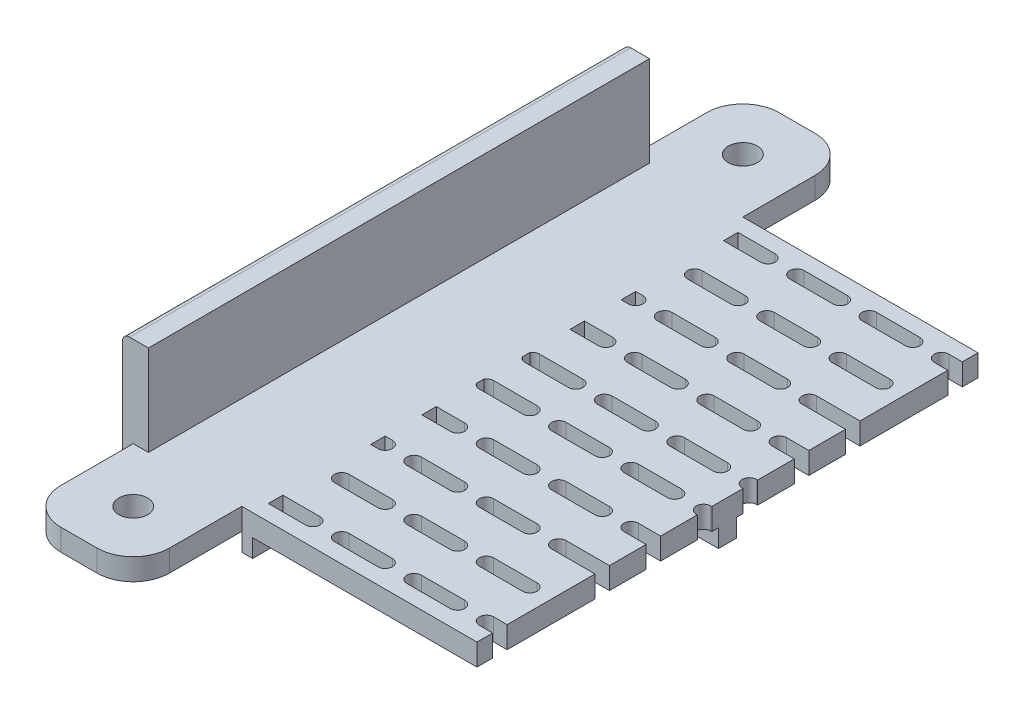
SolidWorks part; units mm, degrees
ref_plane "前视基准面" through (0, 0, 0) normal (0, 0, 1) x (1, 0, 0)
ref_plane "上视基准面" through (0, 0, 0) normal (0, 1, 0) x (1, 0, 0)
ref_plane "右视基准面" through (0, 0, 0) normal (1, 0, 0) x (0, 0, -1)
sketch "草图1" plane through (0, 0, 0) normal (0, 1, 0) x (1, 0, 0)
  line L0 (95.5, 69.25) -> (95.5, -69.25)
  line L1 (90.5, 64.25) -> (-90.5, 64.25)
  line L2 (90.5, 64.25) -> (90.5, -64.25)
  line L3 (90.5, -64.25) -> (-90.5, -64.25)
  line L4 (-90.5, 64.25) -> (-90.5, -64.25)
  line L5 (90.5, 64.25) -> (-90.5, -64.25) construction
  line L6 (90.5, -64.25) -> (-90.5, 64.25) construction
  line L7 (95.5, -69.25) -> (-95.5, -69.25)
  line L8 (-95.5, 69.25) -> (-95.5, -69.25)
  line L9 (95.5, 69.25) -> (-95.5, 69.25)
  point P0 (0, 0)
  dimension "D1" = 5
extrude "凸台-拉伸1" add sketch "草图1" along normal blind 20
sketch "草图2" plane through (0, 0, 0) normal (0, -1, 0) x (1, 0, 0)
  line L4 (-95.5, -69.25) -> (95.5, -69.25)
  line L5 (95.5, -69.25) -> (95.5, 69.25)
  line L6 (95.5, 69.25) -> (-95.5, 69.25)
  line L7 (-95.5, 69.25) -> (-95.5, -69.25)
  line L8 (-95.5, -69.25) -> (95.5, -69.25)
  line L9 (95.5, -69.25) -> (95.5, 69.25)
  line L10 (95.5, 69.25) -> (-95.5, 69.25)
  line L11 (-95.5, 69.25) -> (-95.5, -69.25)
  dimension "D1" = 0
extrude "凸台-拉伸2" add sketch "草图2" along normal blind 5
sketch "草图3" plane through (0, 0, -64.25) normal (0, 0, 1) x (1, 0, 0)
  line L4 (-90.5, 0) -> (90.5, 0)
  line L5 (90.5, 0) -> (90.5, 20)
  line L6 (90.5, 20) -> (-90.5, 20)
  line L7 (-90.5, 20) -> (-90.5, 0)
  line L8 (-90.5, 0) -> (90.5, 0)
  line L9 (90.5, 0) -> (90.5, 20)
  line L10 (90.5, 20) -> (-90.5, 20)
  line L11 (-90.5, 20) -> (-90.5, 0)
  dimension "D1" = 0
extrude "切除-拉伸1" cut sketch "草图3" against normal blind 49 and the other way blind 153
sketch "草图4" plane through (0, -5, 0) normal (0, -1, 0) x (1, 0, 0)
  line L0 (-95.5, 0) -> (-47.5, 0) construction
  line L1 (-47.5, 103) -> (47.5, 103) construction
  line L2 (-47.5, 103) -> (-47.5, -103) construction
  line L3 (-47.5, -103) -> (47.5, -103) construction
  line L4 (47.5, 103) -> (47.5, -103) construction
  line L5 (-47.5, 103) -> (47.5, -103) construction
  line L6 (-47.5, -103) -> (47.5, 103) construction
  line L7 (-95.5, 69.25) -> (-95.5, -69.25) construction
  line L8 (-95.5, 0) -> (-95.5, -35)
  line L9 (-95.5, -35) -> (-90.5, -35)
  line L10 (-90.5, -35) -> (-90.5, 35)
  line L11 (-90.5, 35) -> (-95.5, 35)
  line L12 (-95.5, 35) -> (-95.5, 0)
  line L13 (0, 0) -> (0, 35) construction
  line L14 (95.5, 35) -> (95.5, 0)
  line L15 (90.5, 35) -> (95.5, 35)
  line L16 (90.5, -35) -> (90.5, 35)
  line L17 (95.5, -35) -> (90.5, -35)
  line L18 (95.5, 0) -> (95.5, -35)
  point P0 (0, 0)
extrude "凸台-拉伸3" add sketch "草图4" along normal blind 49
sketch "草图5" plane through (0, -54, 0) normal (0, -1, 0) x (1, 0, 0)
  line L4 (-95.5, 35) -> (-95.5, -35)
  line L5 (-95.5, -35) -> (-90.5, -35)
  line L6 (-90.5, -35) -> (-90.5, 35)
  line L7 (-90.5, 35) -> (-95.5, 35)
  line L8 (-95.5, 35) -> (-95.5, -35)
  line L9 (-95.5, -35) -> (-90.5, -35)
  line L10 (-90.5, -35) -> (-90.5, 35)
  line L11 (-90.5, 35) -> (-95.5, 35)
  line L12 (95.5, 35) -> (90.5, 35)
  line L13 (90.5, 35) -> (90.5, -35)
  line L14 (90.5, -35) -> (95.5, -35)
  line L15 (95.5, -35) -> (95.5, 35)
  line L16 (95.5, 35) -> (90.5, 35)
  line L17 (90.5, 35) -> (90.5, -35)
  line L18 (90.5, -35) -> (95.5, -35)
  line L19 (95.5, -35) -> (95.5, 35)
  dimension "D1" = 0
  dimension "D2" = 0
extrude "凸台-拉伸4" add sketch "草图5" along normal blind 34
sketch "草图7" plane through (-95.5, 0, 0) normal (-1, 0, 0) x (0, 0, 1)
  line L0 (35, -88) -> (-35, -88)
  line L1 (-35, -88) -> (-35, -83)
  line L2 (-35, -88) -> (-35, -5) construction
  line L3 (-35, -83) -> (35, -83)
  line L4 (35, -88) -> (35, -5) construction
  line L5 (35, -83) -> (35, -88)
extrude "凸台-拉伸5" add sketch "草图7" along normal blind 37
sketch "草图8" plane through (95.5, 0, 0) normal (1, 0, 0) x (0, 0, -1)
  line L4 (-35, -83) -> (-35, -88)
  line L5 (35, -83) -> (-35, -83)
  line L6 (35, -88) -> (35, -83)
  line L7 (-35, -88) -> (35, -88)
  line L8 (-35, -83) -> (-35, -88)
  line L9 (35, -83) -> (-35, -83)
  line L10 (35, -88) -> (35, -83)
  line L11 (-35, -88) -> (35, -88)
  dimension "D1" = 0
extrude "凸台-拉伸6" add sketch "草图8" along normal blind 37
sketch "草图12" plane through (0, -5, 0) normal (0, -1, 0) x (1, 0, 0)
  line L0 (0, 0) -> (0, -50.9491) construction
  line L1 (0, 0) -> (21.7152, 0) construction
  line L6 (90.5, 35) -> (95.5, 35)
  line L7 (90.5, 35) -> (95.5, 35)
  line L8 (95.5, -69.25) -> (95.5, -35)
  line L9 (95.5, -35) -> (90.5, -35)
  line L10 (90.5, -35) -> (90.5, 35)
  line L11 (95.5, 35) -> (95.5, 69.25)
  line L15 (95.5, -35) -> (90.5, -35) construction
  line L16 (90.5, -35) -> (90.5, 35) construction
  line L20 (95.5, -69.25) -> (95.5, -35)
  line L27 (95.5, 35) -> (95.5, 69.25)
  line L28 (95.5, 69.25) -> (-95.5, 69.25)
  line L29 (95.5, 69.25) -> (-95.5, 69.25)
  line L30 (-95.5, 69.25) -> (-95.5, 35)
  line L31 (-95.5, 69.25) -> (-95.5, 35)
  line L32 (-95.5, 35) -> (-90.5, 35)
  line L33 (-95.5, 35) -> (-90.5, 35)
  line L34 (-90.5, 35) -> (-90.5, -35)
  line L35 (-90.5, 35) -> (-90.5, -35)
  line L36 (-90.5, -35) -> (-95.5, -35)
  line L37 (-90.5, -35) -> (-95.5, -35)
  line L38 (-95.5, -35) -> (-95.5, -69.25)
  line L39 (-95.5, -35) -> (-95.5, -69.25)
  line L40 (-95.5, -69.25) -> (95.5, -69.25)
  line L41 (-95.5, -69.25) -> (95.5, -69.25)
  circle A0 centre (48, -35) radius 12.5
  circle A1 centre (-48, -35) radius 12.5
  circle A2 centre (48, 35) radius 12.5
  circle A3 centre (-48, 35) radius 12.5
  dimension "D1" = 0
sketch "草图16" plane through (0, -88, 0) normal (0, -1, 0) x (1, 0, 0)
  line L0 (132.5, 35) -> (117.5, 35)
  line L1 (132.5, 35) -> (90.5, 35) construction
  line L2 (117.5, 35) -> (117.5, -35)
  line L3 (90.5, -35) -> (132.5, -35) construction
  line L4 (117.5, -35) -> (132.5, -35)
  line L5 (132.5, -35) -> (132.5, 35)
  line L6 (-132.5, -35) -> (-117.5, -35)
  line L7 (-132.5, -35) -> (-90.5, -35) construction
  line L8 (-117.5, -35) -> (-117.5, 35)
  line L9 (-90.5, 35) -> (-132.5, 35) construction
  line L10 (-117.5, 35) -> (-132.5, 35)
  line L11 (-132.5, 35) -> (-132.5, -35)
extrude "切除-拉伸7" cut sketch "草图16" against normal blind 62
extrude "切除-拉伸9" cut sketch "草图12" against normal blind 20 contours A0 | A1 | A3 | A2
sketch "草图19" plane through (117.5, 0, 0) normal (1, 0, 0) x (0, 0, -1)
  line L4 (-35, -83) -> (-35, -88)
  line L5 (-35, -88) -> (35, -88)
  line L6 (35, -88) -> (35, -83)
  line L7 (35, -83) -> (-35, -83)
  line L8 (-35, -83) -> (-35, -88)
  line L9 (-35, -88) -> (35, -88)
  line L10 (35, -88) -> (35, -83)
  line L11 (35, -83) -> (-35, -83)
  dimension "D1" = 0
extrude "切除-拉伸10" cut sketch "草图19" against normal blind 3.5
sketch "草图20" plane through (-117.5, 0, 0) normal (-1, 0, 0) x (0, 0, 1)
  line L4 (-35, -83) -> (-35, -88)
  line L5 (-35, -88) -> (35, -88)
  line L6 (35, -88) -> (35, -83)
  line L7 (35, -83) -> (-35, -83)
  line L8 (-35, -83) -> (-35, -88)
  line L9 (-35, -88) -> (35, -88)
  line L10 (35, -88) -> (35, -83)
  line L11 (35, -83) -> (-35, -83)
  dimension "D1" = 0
extrude "切除-拉伸11" cut sketch "草图20" against normal blind 3.5
sketch "草图21" plane through (0, -83, 0) normal (0, 1, 0) x (1, 0, 0)
  line L0 (-114, 0) -> (-95.5, 0) construction
  line L1 (-114, -35) -> (-114, 35) construction
  line L2 (-95.5, -35) -> (-95.5, 35) construction
  line L3 (-104.75, 0) -> (-104.75, -35) construction
  line L4 (-114, -35) -> (-95.5, -35) construction
  line L5 (0, 0) -> (0, 27.7926) construction
  circle A0 centre (-104.75, -17.5) radius 4
  circle A1 centre (-104.75, 17.5) radius 4
  circle A2 centre (104.75, -17.5) radius 4
  circle A3 centre (104.75, 17.5) radius 4
extrude "切除-拉伸12" cut sketch "草图21" against normal through all
fillet "圆角5" radius 10 4 edges at (114, -85.5, -35) (114, -85.5, 35) (-114, -85.5, 35) (-114, -85.5, -35)
sketch "草图22" plane through (90.5, 0, 0) normal (-1, 0, 0) x (0, 0, 1)
  line L6 (35, -88) -> (35, -5)
  line L7 (35, -5) -> (-35, -5)
  line L10 (-35, -5) -> (-35, -88)
  line L11 (-35, -88) -> (35, -88)
  line L12 (35, -88) -> (35, -5)
  line L13 (35, -5) -> (-35, -5)
  line L16 (-35, -5) -> (-35, -88)
  line L17 (-35, -88) -> (35, -88)
  dimension "D1" = 0
extrude "切除-拉伸13" cut sketch "草图22" against normal blind 54
sketch "草图23" plane through (-90.5, 0, 0) normal (1, 0, 0) x (0, 0, -1)
  line L6 (35, -5) -> (-35, -5)
  line L7 (-35, -5) -> (-35, -88)
  line L8 (-35, -88) -> (35, -88)
  line L9 (35, -88) -> (35, -5)
  line L12 (35, -5) -> (-35, -5)
  line L13 (-35, -5) -> (-35, -88)
  line L14 (-35, -88) -> (35, -88)
  line L15 (35, -88) -> (35, -5)
  dimension "D1" = 0
extrude "切除-拉伸14" cut sketch "草图23" against normal blind 54
sketch "草图24" plane through (0, -5, 0) normal (0, -1, 0) x (1, 0, 0)
  circle A1 centre (80.5, 18.25) radius 2
  circle A3 centre (80.5, -19.75) radius 2
extrude "切除-拉伸15" cut sketch "草图24" against normal blind 10
sketch "草图25" plane through (0, 0, 0) normal (0, 1, 0) x (1, 0, 0)
  circle A0 centre (80.5, -18.25) radius 4
  circle A1 centre (80.5, 19.75) radius 4
sketch "草图26" plane through (0, 0, 0) normal (0, 1, 0) x (1, 0, 0)
  line L4 (90.5, -69.25) -> (90.5, 69.25)
  line L5 (90.5, 69.25) -> (-90.5, 69.25)
  line L6 (-90.5, 69.25) -> (-90.5, -69.25)
  line L7 (-90.5, -69.25) -> (90.5, -69.25)
  line L8 (90.5, -69.25) -> (90.5, 69.25)
  line L9 (90.5, 69.25) -> (-90.5, 69.25)
  line L10 (-90.5, 69.25) -> (-90.5, -69.25)
  line L11 (-90.5, -69.25) -> (90.5, -69.25)
  circle A0 centre (48, -35) radius 12.5 construction
  circle A1 centre (48, -35) radius 12.5
  circle A2 centre (48, 35) radius 12.5 construction
  circle A3 centre (48, 35) radius 12.5
  circle A4 centre (-48, -35) radius 12.5 construction
  circle A5 centre (-48, -35) radius 12.5
  circle A6 centre (-48, 35) radius 12.5 construction
  circle A7 centre (-48, 35) radius 12.5
  dimension "D1" = 0
extrude "凸台-拉伸8" add sketch "草图26" along normal blind 1
extrude "切除-拉伸16" cut sketch "草图25" along normal blind 1 and the other way blind 4
mirror "镜向1" about plane through (0, 0, 0) normal (1, 0, 0) of "切除-拉伸15", "切除-拉伸16"
sketch "草图28" plane through (0, 1, 0) normal (0, 1, 0) x (1, 0, 0)
  circle A0 centre (-80.5, -18.25) radius 4 construction
  circle A1 centre (-80.5, -18.25) radius 4
  circle A2 centre (-80.5, 19.75) radius 4 construction
  circle A3 centre (-80.5, 19.75) radius 4
  circle A4 centre (80.5, -18.25) radius 4 construction
  circle A5 centre (80.5, -18.25) radius 4
  circle A6 centre (80.5, 19.75) radius 4 construction
  circle A7 centre (80.5, 19.75) radius 4
extrude "凸台-拉伸9" add sketch "草图28" against normal up to surface (6 mm away) up to face at (-80.5, -5, 16.25)
sketch "草图29" plane through (0, -5, 0) normal (0, -1, 0) x (1, 0, 0)
  line L0 (95.5, 69.25) -> (95, 69.25)
  line L1 (-95, 0) -> (-95, 69.25)
  line L2 (95.5, 69.25) -> (-95.5, 69.25) construction
  line L3 (-95, 69.25) -> (-95.5, 69.25)
  line L4 (-95.5, 69.25) -> (-95.5, -69.25)
  line L5 (-95.5, -69.25) -> (-95, -69.25)
  line L6 (-95.5, -69.25) -> (95.5, -69.25) construction
  line L7 (-95, -69.25) -> (-95, 0)
  line L8 (95, 69.25) -> (95, -69.25)
  line L9 (95, -69.25) -> (95.5, -69.25)
  line L10 (95.5, -69.25) -> (95.5, 69.25)
extrude "切除-拉伸18" cut sketch "草图29" against normal blind 50
sketch "草图31" plane through (0, -5, 0) normal (0, -1, 0) x (1, 0, 0)
  line L0 (-95, 69.25) -> (-95, 89.25)
  line L1 (-85, 99.25) -> (-75, 99.25)
  line L2 (-65, 89.25) -> (-65, 69.25)
  line L3 (95, 69.25) -> (-95, 69.25) construction
  line L4 (-65, 69.25) -> (-95, 69.25)
  line L5 (-80, 99.25) -> (-80, 69.25) construction
  line L6 (-80, 84.25) -> (-65, 84.25) construction
  line L7 (0, 0) -> (19.0311, 0) construction
  line L8 (0, 0) -> (0, -16.3488) construction
  line L9 (-65, -89.25) -> (-65, -69.25)
  line L10 (-85, -99.25) -> (-75, -99.25)
  line L11 (-95, -69.25) -> (-95, -89.25)
  line L12 (-65, -69.25) -> (-95, -69.25)
  line L13 (80, 84.25) -> (65, 84.25) construction
  line L14 (80, 99.25) -> (80, 69.25) construction
  line L15 (65, -69.25) -> (95, -69.25)
  line L16 (95, -69.25) -> (95, -89.25)
  line L17 (85, -99.25) -> (75, -99.25)
  line L18 (65, -89.25) -> (65, -69.25)
  line L19 (65, 69.25) -> (95, 69.25)
  line L20 (65, 89.25) -> (65, 69.25)
  line L21 (85, 99.25) -> (75, 99.25)
  line L22 (95, 69.25) -> (95, 89.25)
  arc A0 (-65, 89.25) -> (-75, 99.25) centre (-75, 89.25) ccw
  arc A1 (-95, 89.25) -> (-85, 99.25) centre (-85, 89.25) cw
  circle A2 centre (-80, 84.25) radius 4
  circle A3 centre (-80, -84.25) radius 4
  arc A4 (-65, -89.25) -> (-75, -99.25) centre (-75, -89.25) cw
  arc A5 (-95, -89.25) -> (-85, -99.25) centre (-85, -89.25) ccw
  arc A6 (95, -89.25) -> (85, -99.25) centre (85, -89.25) cw
  arc A7 (65, -89.25) -> (75, -99.25) centre (75, -89.25) ccw
  circle A8 centre (80, -84.25) radius 4
  circle A9 centre (80, 84.25) radius 4
  arc A10 (95, 89.25) -> (85, 99.25) centre (85, 89.25) ccw
  arc A11 (65, 89.25) -> (75, 99.25) centre (75, 89.25) cw
  dimension "D1" = 10
extrude "凸台-拉伸10" add sketch "草图31" against normal up to surface (6 mm away) up to face at (-48, 1, 47.5)
sketch "草图32" plane through (0, 20, 0) normal (0, 1, 0) x (1, 0, 0)
  line L0 (90.5, 69.25) -> (91.3, 69.25)
  line L4 (95, 69.25) -> (90.5, 69.25) construction
  line L5 (90.5, -69.25) -> (90.5, 69.25) construction
  line L6 (90.5, -69.25) -> (90.5, 69.25)
  line L7 (91.3, 69.25) -> (91.3, -69.25)
  line L8 (90.5, -69.25) -> (95, -69.25) construction
  line L9 (91.3, -69.25) -> (90.5, -69.25)
  line L10 (-90.5, -69.25) -> (-91.3, -69.25)
  line L11 (-95, -69.25) -> (-90.5, -69.25) construction
  line L12 (-91.3, -69.25) -> (-91.3, 69.25)
  line L13 (-90.5, 69.25) -> (-95, 69.25) construction
  line L14 (-91.3, 69.25) -> (-90.5, 69.25)
  line L15 (-90.5, 69.25) -> (-90.5, -69.25) construction
  line L16 (-90.5, 69.25) -> (-90.5, -69.25)
extrude "切除-拉伸19" cut sketch "草图32" against normal up to surface (19 mm away) up to face at (-48, 1, 47.5)
sketch "草图33" plane through (0, 20, 0) normal (0, 1, 0) x (1, 0, 0)
  line L4 (91.3, 69.25) -> (91.3, -69.25)
  line L5 (91.3, -69.25) -> (95, -69.25)
  line L6 (95, -69.25) -> (95, 69.25)
  line L7 (95, 69.25) -> (91.3, 69.25)
  line L8 (91.3, 69.25) -> (91.3, -69.25)
  line L9 (91.3, -69.25) -> (95, -69.25)
  line L10 (95, -69.25) -> (95, 69.25)
  line L11 (95, 69.25) -> (91.3, 69.25)
  line L12 (-91.3, -69.25) -> (-91.3, 69.25)
  line L13 (-91.3, 69.25) -> (-95, 69.25)
  line L14 (-95, 69.25) -> (-95, -69.25)
  line L15 (-95, -69.25) -> (-91.3, -69.25)
  line L16 (-91.3, -69.25) -> (-91.3, 69.25)
  line L17 (-91.3, 69.25) -> (-95, 69.25)
  line L18 (-95, 69.25) -> (-95, -69.25)
  line L19 (-95, -69.25) -> (-91.3, -69.25)
  dimension "D1" = 0
  dimension "D2" = 0
extrude "凸台-拉伸11" add sketch "草图33" along normal blind 6
sketch "草图34" plane through (0, -5, 0) normal (0, -1, 0) x (1, 0, 0)
  circle A0 centre (-48, -35) radius 12.5 construction
  circle A1 centre (-48, -35) radius 12.5
  circle A2 centre (-48, 35) radius 12.5 construction
  circle A3 centre (-48, 35) radius 12.5
  circle A4 centre (48, -35) radius 12.5 construction
  circle A5 centre (48, -35) radius 12.5
  circle A6 centre (48, 35) radius 12.5 construction
  circle A7 centre (48, 35) radius 12.5
extrude "凸台-拉伸12" add sketch "草图34" against normal up to surface (6 mm away) up to face at (0, 1, 0)
sketch "草图35" plane through (0, -5, 0) normal (0, -1, 0) x (1, 0, 0)
  line L0 (65, -69.25) -> (62, -69.25)
  line L2 (65, 69.25) -> (65, -69.25)
  line L6 (-65, -69.25) -> (65, -69.25) construction
  line L8 (62, -69.25) -> (62, 69.25)
  line L9 (65, 69.25) -> (-65, 69.25) construction
  line L10 (62, 69.25) -> (65, 69.25)
  line L11 (-65, -69.25) -> (-62, -69.25)
  line L12 (-62, -69.25) -> (-62, 69.25)
  line L13 (-62, 69.25) -> (-65, 69.25)
  line L14 (-65, 69.25) -> (-65, 89.25) construction
  line L15 (-65, 69.25) -> (-65, -69.25)
  point P0 (0, 0)
extrude "凸台-拉伸13" add sketch "草图35" along normal blind 5
sketch "草图36" plane through (-95, 0, 0) normal (-1, 0, 0) x (0, 0, 1)
  line L0 (-69.25, -10) -> (-69.25, -5) construction
  line L1 (-69.25, -10) -> (-69.25, -5)
  line L2 (69.25, -10) -> (69.25, -5) construction
  line L3 (69.25, -10) -> (69.25, -5)
  line L7 (-69.25, 26) -> (69.25, 26) construction
  line L8 (-69.25, 26) -> (69.25, 26)
  line L9 (69.25, 26) -> (69.25, 1) construction
  line L10 (69.25, 26) -> (69.25, 1)
  line L13 (-69.25, -10) -> (69.25, -10)
  line L16 (-69.25, 26) -> (-69.25, 1) construction
  line L17 (-69.25, 26) -> (-69.25, 1)
  line L18 (-69.25, 1) -> (-69.25, -5)
  line L19 (69.25, -5) -> (69.25, 1)
extrude "凸台-拉伸14" add sketch "草图36" along normal blind 3
sketch "草图37" plane through (-95, 0, 0) normal (1, 0, 0) x (0, 0, -1)
  line L4 (69.25, -5) -> (-69.25, -5)
  line L5 (-69.25, -5) -> (-69.25, -10)
  line L6 (-69.25, -10) -> (69.25, -10)
  line L7 (69.25, -10) -> (69.25, -5)
  line L8 (69.25, -5) -> (-69.25, -5)
  line L9 (-69.25, -5) -> (-69.25, -10)
  line L10 (-69.25, -10) -> (69.25, -10)
  line L11 (69.25, -10) -> (69.25, -5)
  dimension "D1" = 0
extrude "切除-拉伸20" cut sketch "草图37" against normal blind 0.5
mirror "镜向2" about plane through (0, 0, 0) normal (1, 0, 0) of "切除-拉伸20", "凸台-拉伸14"
sketch "草图38" plane through (0, -5, 0) normal (0, -1, 0) x (1, 0, 0)
  line L2 (0, 0) -> (62, 0)
  line L3 (62, 69.25) -> (62, -69.25) construction
  line L4 (0, -2.5) -> (-62, -2.5)
  line L5 (0, -2.5) -> (62, -2.5)
  line L6 (0, 2.5) -> (-62, 2.5)
  line L7 (0, 2.5) -> (62, 2.5)
  line L8 (-62, -69.25) -> (-62, 69.25) construction
  line L9 (-62, -2.5) -> (-62, 2.5)
  line L10 (62, 69.25) -> (62, -69.25) construction
  line L11 (62, 2.5) -> (62, -2.5)
  line L12 (0, 0) -> (-62, 0) construction
  dimension "D1" = 2.5
  dimension "D2" = 2.5
extrude "凸台-拉伸15" add sketch "草图38" along normal up to surface (5 mm away) contours L6 L9 L4 L5 L11 L7 up to face at (-63.5, -10, 0)
sketch "草图40" plane through (0, -5, 0) normal (0, -1, 0) x (1, 0, 0)
  line L0 (0, 0) -> (0, 69.25) construction
  line L1 (62, 69.25) -> (-62, 69.25) construction
  line L2 (0, 34.625) -> (-12, 34.625) construction
  line L3 (0, 34.625) -> (-32.125, 2.5) construction
  line L4 (0, 32.625) -> (-12, 32.625)
  line L5 (0, 36.625) -> (-12, 36.625)
  line L6 (62, 2.5) -> (-62, 2.5) construction
  line L7 (25, 34.625) -> (13, 34.625) construction
  line L8 (25, 32.625) -> (13, 32.625)
  line L9 (25, 36.625) -> (13, 36.625)
  line L10 (50, 34.625) -> (38, 34.625) construction
  line L11 (50, 32.625) -> (38, 32.625)
  line L12 (50, 36.625) -> (38, 36.625)
  line L13 (-25, 34.625) -> (-37, 34.625) construction
  line L14 (-25, 32.625) -> (-37, 32.625)
  line L15 (-25, 36.625) -> (-37, 36.625)
  arc A0 (0, 32.625) -> (0, 36.625) centre (0, 34.625) ccw
  arc A1 (-12, 36.625) -> (-12, 32.625) centre (-12, 34.625) ccw
  arc A2 (25, 32.625) -> (25, 36.625) centre (25, 34.625) ccw
  arc A3 (13, 36.625) -> (13, 32.625) centre (13, 34.625) ccw
  arc A4 (50, 32.625) -> (50, 36.625) centre (50, 34.625) ccw
  arc A5 (38, 36.625) -> (38, 32.625) centre (38, 34.625) ccw
  arc A6 (-25, 32.625) -> (-25, 36.625) centre (-25, 34.625) ccw
  arc A7 (-37, 36.625) -> (-37, 32.625) centre (-37, 34.625) ccw
  point P9 (-6, 34.625)
  point P20 (19, 34.625)
  point P27 (44, 34.625)
  point P34 (-31, 34.625)
  dimension "D1" = 45
  dimension "D2" = 3
  dimension "D3" = 2
extrude "切除-拉伸22" cut sketch "草图40" against normal through all contours L5 A1 L4 A0
sketch "草图41" plane through (0, -5, 0) normal (0, -1, 0) x (1, 0, 0)
  line L0 (0, 0) -> (0, 69.25)
  line L1 (62, 69.25) -> (-62, 69.25) construction
  line L2 (0, 34.625) -> (-32.125, 2.5)
  line L3 (62, 2.5) -> (-62, 2.5) construction
  dimension "D1" = 45
pattern_linear "阵列(线性)1" count 3 spacing 20 along (-0.7071, 0, -0.7071) of "切除-拉伸22"
pattern_linear "阵列(线性)2" count 3 spacing 20 along (0.7071, 0, 0.7071) of "切除-拉伸22"
pattern_linear "阵列(线性)3" count 5 spacing 20 along (1, 0, 0) of "阵列(线性)2", "阵列(线性)1", "切除-拉伸22"
sketch "草图42" plane through (0, 1, 0) normal (0, 1, 0) x (1, 0, 0)
  line L0 (82.1421, -50.7671) -> (91.3, -50.7671) construction
  line L1 (82.1421, -50.7671) -> (91.3, -50.7671)
  line L2 (82.1421, -46.7671) -> (91.3, -46.7671) construction
  line L3 (82.1421, -46.7671) -> (91.3, -46.7671)
  line L4 (94.1421, -46.7671) -> (91.3, -46.7671) construction
  line L5 (94.1421, -46.7671) -> (91.3, -46.7671)
  line L6 (94.1421, -50.7671) -> (91.3, -50.7671) construction
  line L7 (94.1421, -50.7671) -> (91.3, -50.7671)
  line L8 (98, -64.9093) -> (96.2843, -64.9093) construction
  line L9 (98, -64.9093) -> (96.2843, -64.9093)
  line L10 (98, -60.9093) -> (96.2843, -60.9093) construction
  line L11 (98, -60.9093) -> (96.2843, -60.9093)
  line L12 (98, -64.9093) -> (98, -60.9093) construction
  line L13 (98, -64.9093) -> (98, -60.9093)
  line L14 (76.2843, -60.9093) -> (88.2843, -60.9093) construction
  line L15 (76.2843, -60.9093) -> (88.2843, -60.9093)
  line L16 (76.2843, -64.9093) -> (88.2843, -64.9093) construction
  line L17 (76.2843, -64.9093) -> (88.2843, -64.9093)
  line L20 (56.2843, -60.9093) -> (68.2843, -60.9093) construction
  line L21 (65, -60.9093) -> (68.2843, -60.9093)
  line L22 (56.2843, -64.9093) -> (68.2843, -64.9093) construction
  line L23 (65, -64.9093) -> (68.2843, -64.9093)
  line L26 (62.1421, -50.7671) -> (74.1421, -50.7671) construction
  line L27 (62.1421, -46.7671) -> (74.1421, -46.7671) construction
  line L28 (65, -50.7671) -> (74.1421, -50.7671)
  line L29 (65, -46.7671) -> (74.1421, -46.7671)
  line L30 (68, -32.625) -> (80, -32.625) construction
  line L31 (68, -36.625) -> (80, -36.625) construction
  line L32 (68, -32.625) -> (80, -32.625)
  line L33 (68, -36.625) -> (80, -36.625)
  line L34 (53.8579, -22.4829) -> (65.8579, -22.4829) construction
  line L35 (53.8579, -18.4829) -> (65.8579, -18.4829) construction
  line L37 (65, -22.4829) -> (65.8579, -22.4829)
  line L38 (65, -18.4829) -> (65.8579, -18.4829)
  line L44 (62, -64.9093) -> (65, -64.9093)
  line L45 (65, -64.9093) -> (65, -60.9093)
  line L46 (65, -60.9093) -> (62, -60.9093)
  line L47 (62, -60.9093) -> (62, -64.9093)
  line L48 (62, -64.9093) -> (65, -64.9093)
  line L49 (62.1421, -50.7671) -> (65, -50.7671)
  line L50 (65, -60.9093) -> (62, -60.9093)
  line L51 (62, -60.9093) -> (62, -64.9093)
  line L52 (65, -50.7671) -> (65, -46.7671)
  line L53 (65, -46.7671) -> (62.1421, -46.7671)
  line L54 (62, -46.7722) -> (62, -50.7621)
  line L55 (62.1421, -50.7671) -> (65, -50.7671)
  line L56 (62, -22.4829) -> (65, -22.4829)
  line L57 (65, -46.7671) -> (62.1421, -46.7671)
  line L58 (62, -46.7722) -> (62, -50.7621)
  line L59 (65, -22.4829) -> (65, -18.4829)
  line L60 (65, -18.4829) -> (62, -18.4829)
  line L61 (62, -18.4829) -> (62, -22.4829)
  line L62 (62, -22.4829) -> (65, -22.4829)
  line L64 (65, -18.4829) -> (62, -18.4829)
  line L65 (62, -18.4829) -> (62, -22.4829)
  arc A0 (82.1421, -46.7671) -> (82.1421, -50.7671) centre (82.1421, -48.7671) ccw construction
  arc A1 (82.1421, -46.7671) -> (82.1421, -50.7671) centre (82.1421, -48.7671) ccw
  arc A2 (95.5, -50.2355) -> (95.5, -47.2987) centre (94.1421, -48.7671) ccw construction
  arc A3 (95.5, -50.2355) -> (95.5, -47.2987) centre (94.1421, -48.7671) ccw
  arc A4 (95.5, -47.2987) -> (94.1421, -46.7671) centre (94.1421, -48.7671) ccw construction
  arc A5 (95.5, -47.2987) -> (94.1421, -46.7671) centre (94.1421, -48.7671) ccw
  arc A6 (94.1421, -50.7671) -> (95.5, -50.2355) centre (94.1421, -48.7671) ccw construction
  arc A7 (94.1421, -50.7671) -> (95.5, -50.2355) centre (94.1421, -48.7671) ccw
  arc A8 (96.2843, -60.9093) -> (96.2843, -64.9093) centre (96.2843, -62.9093) ccw construction
  arc A9 (96.2843, -60.9093) -> (96.2843, -64.9093) centre (96.2843, -62.9093) ccw
  arc A10 (88.2843, -64.9093) -> (88.2843, -60.9093) centre (88.2843, -62.9093) ccw construction
  arc A11 (88.2843, -64.9093) -> (88.2843, -60.9093) centre (88.2843, -62.9093) ccw
  arc A12 (76.2843, -60.9093) -> (76.2843, -64.9093) centre (76.2843, -62.9093) ccw construction
  arc A13 (76.2843, -60.9093) -> (76.2843, -64.9093) centre (76.2843, -62.9093) ccw
  arc A14 (68.2843, -64.9093) -> (68.2843, -60.9093) centre (68.2843, -62.9093) ccw construction
  arc A15 (68.2843, -64.9093) -> (68.2843, -60.9093) centre (68.2843, -62.9093) ccw
  arc A16 (74.1421, -50.7671) -> (74.1421, -46.7671) centre (74.1421, -48.7671) ccw construction
  arc A17 (74.1421, -50.7671) -> (74.1421, -46.7671) centre (74.1421, -48.7671) ccw
  arc A18 (68, -32.625) -> (68, -36.625) centre (68, -34.625) ccw construction
  arc A19 (80, -36.625) -> (80, -32.625) centre (80, -34.625) ccw construction
  arc A20 (68, -32.625) -> (68, -36.625) centre (68, -34.625) ccw
  arc A21 (80, -36.625) -> (80, -32.625) centre (80, -34.625) ccw
  arc A22 (65.8579, -22.4829) -> (65.8579, -18.4829) centre (65.8579, -20.4829) ccw construction
  arc A23 (65.8579, -22.4829) -> (65.8579, -18.4829) centre (65.8579, -20.4829) ccw
  arc A26 (62, -50.7621) -> (62.1421, -50.7671) centre (62.1421, -48.7671) ccw
  arc A27 (62.1421, -46.7671) -> (62, -46.7722) centre (62.1421, -48.7671) ccw
  arc A28 (62, -50.7621) -> (62.1421, -50.7671) centre (62.1421, -48.7671) ccw
  arc A29 (62.1421, -46.7671) -> (62, -46.7722) centre (62.1421, -48.7671) ccw
  dimension "D1" = 0
  dimension "D2" = 0
  dimension "D3" = 0
extrude "凸台-拉伸16" add sketch "草图42" against normal up to surface (6 mm away) up to face at (63.5, -5, 62.9093)
sketch "草图43" plane through (0, 1, 0) normal (0, 1, 0) x (1, 0, 0)
  line L0 (94.1421, -46.7671) -> (91.3, -46.7671) construction
  line L1 (94.1421, -46.7671) -> (91.3, -46.7671)
  line L2 (94.1421, -50.7671) -> (91.3, -50.7671) construction
  line L3 (96.2843, -64.9093) -> (98, -64.9093)
  line L4 (98, -64.9093) -> (98, -60.9093)
  line L5 (98, -60.9093) -> (96.2843, -60.9093)
  line L6 (96.2843, -64.9093) -> (98, -64.9093)
  line L7 (98, -64.9093) -> (98, -60.9093)
  line L8 (98, -60.9093) -> (96.2843, -60.9093)
  line L9 (94.1421, -50.7671) -> (91.3, -50.7671)
  line L10 (91.3, -50.7671) -> (91.3, -46.7671)
  arc A0 (94.1421, -50.7671) -> (94.1421, -46.7671) centre (94.1421, -48.7671) ccw construction
  arc A1 (96.2843, -60.9093) -> (96.2843, -64.9093) centre (96.2843, -62.9093) ccw
  arc A2 (96.2843, -60.9093) -> (96.2843, -64.9093) centre (96.2843, -62.9093) ccw
  arc A3 (94.1421, -50.7671) -> (94.1421, -46.7671) centre (94.1421, -48.7671) ccw
  dimension "D1" = 0
extrude "凸台-拉伸17" add sketch "草图43" along normal up to surface (25 mm away)
pattern_linear "阵列(线性)4" count 5 spacing 20 along (-1, 0, 0) of "阵列(线性)1", "阵列(线性)2", "切除-拉伸22"
sketch "草图44" plane through (0, 1, 0) normal (0, 1, 0) x (1, 0, 0)
  line L0 (-63.7157, -64.9093) -> (-51.7157, -64.9093) construction
  line L1 (-63.7157, -60.9093) -> (-51.7157, -60.9093) construction
  line L2 (-62, -60.9093) -> (-62, -64.9093) construction
  line L3 (-62, -32.625) -> (-62, -36.625) construction
  line L4 (-72, -32.625) -> (-60, -32.625) construction
  line L5 (-72, -36.625) -> (-60, -36.625) construction
  line L7 (-77.8579, -50.7671) -> (-65.8579, -50.7671) construction
  line L8 (-77.8579, -46.7671) -> (-65.8579, -46.7671) construction
  line L9 (-63.7157, -64.9093) -> (-62, -64.9093)
  line L10 (-63.7157, -60.9093) -> (-62, -60.9093)
  line L11 (-62, -60.9093) -> (-62, -64.9093)
  line L12 (-62, -32.625) -> (-62, -36.625)
  line L13 (-72, -32.625) -> (-62, -32.625)
  line L14 (-72, -36.625) -> (-62, -36.625)
  line L16 (-77.8579, -50.7671) -> (-65.8579, -50.7671)
  line L17 (-77.8579, -46.7671) -> (-65.8579, -46.7671)
  line L18 (-98, -4.3407) -> (-98, -8.3407) construction
  line L19 (-62, -18.4829) -> (-62, -22.4829) construction
  line L20 (-66.1421, -22.4829) -> (-54.1421, -22.4829) construction
  line L21 (-66.1421, -18.4829) -> (-54.1421, -18.4829) construction
  line L22 (-62, -5.313) -> (-62, -7.3685) construction
  line L23 (-80.2843, -8.3407) -> (-68.2843, -8.3407) construction
  line L24 (-80.2843, -4.3407) -> (-68.2843, -4.3407) construction
  line L25 (-91.3, -8.3407) -> (-88.2843, -8.3407) construction
  line L26 (-91.3, -4.3407) -> (-88.2843, -4.3407) construction
  line L27 (-91.3, -4.3407) -> (-98, -4.3407) construction
  line L28 (-91.3, -8.3407) -> (-98, -8.3407) construction
  line L29 (-98, -4.3407) -> (-98, -8.3407)
  line L30 (-91.3, -8.3407) -> (-98, -8.3407)
  line L31 (-91.3, -4.3407) -> (-98, -4.3407)
  line L32 (-91.3, -4.3407) -> (-88.2843, -4.3407)
  line L33 (-91.3, -8.3407) -> (-88.2843, -8.3407)
  line L34 (-80.2843, -4.3407) -> (-68.2843, -4.3407)
  line L35 (-80.2843, -8.3407) -> (-68.2843, -8.3407)
  line L36 (-62, -5.313) -> (-62, -7.3685)
  line L37 (-66.1421, -18.4829) -> (-62, -18.4829)
  line L38 (-66.1421, -22.4829) -> (-62, -22.4829)
  line L39 (-62, -18.4829) -> (-62, -22.4829)
  line L40 (-91.3, -36.625) -> (-80, -36.625) construction
  line L41 (-92, -36.625) -> (-91.3, -36.625) construction
  line L42 (-92, -32.625) -> (-91.3, -32.625) construction
  line L43 (-91.3, -32.625) -> (-80, -32.625) construction
  line L44 (-86.1421, -22.4829) -> (-74.1421, -22.4829) construction
  line L45 (-86.1421, -18.4829) -> (-74.1421, -18.4829) construction
  line L46 (-94.1421, -22.4829) -> (-98, -22.4829) construction
  line L47 (-94.1421, -18.4829) -> (-98, -18.4829) construction
  line L48 (-98, -18.4829) -> (-98, -22.4829) construction
  line L49 (-91.3, -36.625) -> (-80, -36.625)
  line L50 (-92, -36.625) -> (-91.3, -36.625)
  line L51 (-92, -32.625) -> (-91.3, -32.625)
  line L52 (-91.3, -32.625) -> (-80, -32.625)
  line L53 (-86.1421, -22.4829) -> (-74.1421, -22.4829)
  line L54 (-86.1421, -18.4829) -> (-74.1421, -18.4829)
  line L55 (-94.1421, -22.4829) -> (-98, -22.4829)
  line L56 (-94.1421, -18.4829) -> (-98, -18.4829)
  line L57 (-98, -18.4829) -> (-98, -22.4829)
  arc A0 (-63.7157, -60.9093) -> (-63.7157, -64.9093) centre (-63.7157, -62.9093) ccw construction
  arc A1 (-72, -32.625) -> (-72, -36.625) centre (-72, -34.625) ccw construction
  arc A2 (-65.8579, -50.7671) -> (-65.8579, -46.7671) centre (-65.8579, -48.7671) ccw construction
  arc A3 (-77.8579, -46.7671) -> (-77.8579, -50.7671) centre (-77.8579, -48.7671) ccw construction
  arc A4 (-63.7157, -60.9093) -> (-63.7157, -64.9093) centre (-63.7157, -62.9093) ccw
  arc A5 (-72, -32.625) -> (-72, -36.625) centre (-72, -34.625) ccw
  arc A7 (-77.8579, -46.7671) -> (-77.8579, -50.7671) centre (-77.8579, -48.7671) ccw
  arc A8 (-66.1421, -18.4829) -> (-66.1421, -22.4829) centre (-66.1421, -20.4829) ccw construction
  arc A9 (-60.2843, -4.3407) -> (-60.2843, -8.3407) centre (-60.2843, -6.3407) ccw construction
  arc A10 (-68.2843, -8.3407) -> (-68.2843, -4.3407) centre (-68.2843, -6.3407) ccw construction
  arc A11 (-80.2843, -4.3407) -> (-80.2843, -8.3407) centre (-80.2843, -6.3407) ccw construction
  arc A12 (-88.2843, -8.3407) -> (-88.2843, -4.3407) centre (-88.2843, -6.3407) ccw construction
  arc A13 (-88.2843, -8.3407) -> (-88.2843, -4.3407) centre (-88.2843, -6.3407) ccw
  arc A14 (-80.2843, -4.3407) -> (-80.2843, -8.3407) centre (-80.2843, -6.3407) ccw
  arc A15 (-68.2843, -8.3407) -> (-68.2843, -4.3407) centre (-68.2843, -6.3407) ccw
  arc A16 (-62, -5.313) -> (-62, -7.3685) centre (-60.2843, -6.3407) ccw
  arc A17 (-66.1421, -18.4829) -> (-66.1421, -22.4829) centre (-66.1421, -20.4829) ccw
  arc A18 (-80, -36.625) -> (-80, -32.625) centre (-80, -34.625) ccw construction
  arc A19 (-92, -32.625) -> (-92, -36.625) centre (-92, -34.625) ccw construction
  arc A20 (-74.1421, -22.4829) -> (-74.1421, -18.4829) centre (-74.1421, -20.4829) ccw construction
  arc A21 (-86.1421, -18.4829) -> (-86.1421, -22.4829) centre (-86.1421, -20.4829) ccw construction
  arc A22 (-94.1421, -22.4829) -> (-94.1421, -18.4829) centre (-94.1421, -20.4829) ccw construction
  arc A23 (-80, -36.625) -> (-80, -32.625) centre (-80, -34.625) ccw
  arc A24 (-92, -32.625) -> (-92, -36.625) centre (-92, -34.625) ccw
  arc A25 (-74.1421, -22.4829) -> (-74.1421, -18.4829) centre (-74.1421, -20.4829) ccw
  arc A26 (-86.1421, -18.4829) -> (-86.1421, -22.4829) centre (-86.1421, -20.4829) ccw
  arc A27 (-94.1421, -22.4829) -> (-94.1421, -18.4829) centre (-94.1421, -20.4829) ccw
  arc A29 (-65.8579, -50.7671) -> (-65.8579, -46.7671) centre (-65.8579, -48.7671) ccw
extrude "凸台-拉伸18" add sketch "草图44" against normal up to surface (6 mm away)
sketch "草图45" plane through (0, 1, 0) normal (0, 1, 0) x (1, 0, 0)
  line L0 (-91.3, -4.3407) -> (-98, -4.3407) construction
  line L1 (-91.3, -4.3407) -> (-98, -4.3407)
  line L2 (-91.3, -8.3407) -> (-98, -8.3407) construction
  line L3 (-91.3, -8.3407) -> (-98, -8.3407)
  line L4 (-98, -4.3407) -> (-98, -8.3407) construction
  line L5 (-98, -4.3407) -> (-98, -8.3407)
  line L6 (-92, -32.625) -> (-91.3, -32.625) construction
  line L7 (-92, -32.625) -> (-91.3, -32.625)
  line L8 (-92, -36.625) -> (-91.3, -36.625) construction
  line L9 (-94.1421, -18.4829) -> (-98, -18.4829)
  line L10 (-98, -18.4829) -> (-98, -22.4829)
  line L11 (-98, -22.4829) -> (-94.1421, -22.4829)
  line L12 (-94.1421, -18.4829) -> (-98, -18.4829)
  line L13 (-98, -18.4829) -> (-98, -22.4829)
  line L14 (-98, -22.4829) -> (-94.1421, -22.4829)
  line L15 (-92, -36.625) -> (-91.3, -36.625)
  line L16 (-91.3, -8.3407) -> (-91.3, -4.3407)
  line L17 (-91.3, -32.625) -> (-91.3, -36.625)
  arc A0 (-92, -32.625) -> (-92, -36.625) centre (-92, -34.625) ccw construction
  arc A1 (-94.1421, -22.4829) -> (-94.1421, -18.4829) centre (-94.1421, -20.4829) ccw
  arc A2 (-94.1421, -22.4829) -> (-94.1421, -18.4829) centre (-94.1421, -20.4829) ccw
  arc A3 (-92, -32.625) -> (-92, -36.625) centre (-92, -34.625) ccw
  dimension "D1" = 0
extrude "凸台-拉伸19" add sketch "草图45" along normal up to surface (25 mm away) up to face at (-94.65, 26, -32.4546)
mirror "镜向5" about plane through (0, 0, 0) normal (0, 0, 1) of "阵列(线性)4", "阵列(线性)3", "阵列(线性)2", "阵列(线性)1", "切除-拉伸22"
sketch "草图46" plane through (0, 1, 0) normal (0, 1, 0) x (1, 0, 0)
  line L10 (62.2843, 60.9093) -> (62.2843, 69.25)
  line L11 (56.2843, 60.9093) -> (68.2843, 60.9093) construction
  line L12 (65, 69.25) -> (-65, 69.25) construction
  line L13 (98, 64.9093) -> (98, 69.25) construction
  line L14 (98, 64.9093) -> (98, 69.25)
  line L15 (62.2843, 69.25) -> (98, 69.25)
  line L16 (62.2843, 60.9093) -> (62.2843, 4.433)
  line L17 (62.2843, 4.433) -> (98, 4.433)
  line L18 (98, 4.433) -> (98, 64.9093)
  line L19 (0, 0) -> (0, 15.6294) construction
  line L20 (-62.2843, 4.433) -> (-98, 4.433)
  line L21 (-62.2843, 60.9093) -> (-62.2843, 4.433)
  line L22 (-62.2843, 60.9093) -> (-62.2843, 69.25)
  line L23 (-62.2843, 69.25) -> (-98, 69.25)
  line L24 (-98, 64.9093) -> (-98, 69.25)
  line L25 (-98, 4.433) -> (-98, 64.9093)
extrude "凸台-拉伸20" add sketch "草图46" against normal up to surface (6 mm away) up to face at (-34.2843, -5, -6.3407)
sketch "草图47" plane through (0, 1, 0) normal (0, 1, 0) x (1, 0, 0)
  line L0 (-98, 4.433) -> (-98, 4.3407) construction
  line L1 (-62, 5.313) -> (-62, 7.3685)
  line L2 (-62, 5.313) -> (-62, 7.3685)
  line L3 (-98, 4.433) -> (-98, 4.3407)
  line L4 (-62, 22.4829) -> (-62.2843, 22.4829)
  line L5 (-62.2843, 22.4829) -> (-62.2843, 18.4829)
  line L6 (-62.2843, 18.4829) -> (-62, 18.4829)
  line L7 (-62, 18.4829) -> (-62, 22.4829)
  line L8 (-62, 22.4829) -> (-62.2843, 22.4829)
  line L9 (-62.2843, 22.4829) -> (-62.2843, 18.4829)
  line L10 (-62.2843, 18.4829) -> (-62, 18.4829)
  line L11 (-62, 18.4829) -> (-62, 22.4829)
  line L12 (-98, 4.433) -> (-87.6837, 4.433) construction
  line L13 (-98, 4.433) -> (-87.6837, 4.433)
  line L14 (-62, 36.625) -> (-62.2843, 36.625)
  line L15 (-62.2843, 36.625) -> (-62.2843, 32.625)
  line L16 (-62.2843, 32.625) -> (-62, 32.625)
  line L17 (-62, 32.625) -> (-62, 36.625)
  line L18 (-62, 36.625) -> (-62.2843, 36.625)
  line L19 (-62.2843, 36.625) -> (-62.2843, 32.625)
  line L20 (-62.2843, 32.625) -> (-62, 32.625)
  line L21 (-62, 32.625) -> (-62, 36.625)
  line L22 (-62, 64.9093) -> (-62.2843, 64.9093)
  line L23 (-62.2843, 64.9093) -> (-62.2843, 60.9093)
  line L24 (-62.2843, 60.9093) -> (-62, 60.9093)
  line L25 (-62, 60.9093) -> (-62, 64.9093)
  line L26 (-62, 64.9093) -> (-62.2843, 64.9093)
  line L27 (-62.2843, 64.9093) -> (-62.2843, 60.9093)
  line L28 (-62.2843, 60.9093) -> (-62, 60.9093)
  line L29 (-62, 60.9093) -> (-62, 64.9093)
  line L30 (-91.3, 4.3407) -> (-88.2843, 4.3407) construction
  line L31 (-91.3, 4.3407) -> (-88.2843, 4.3407)
  line L32 (-91.3, 4.3407) -> (-98, 4.3407) construction
  line L33 (-91.3, 4.3407) -> (-98, 4.3407)
  line L34 (-80.8849, 4.433) -> (-67.6837, 4.433) construction
  line L35 (-80.8849, 4.433) -> (-67.6837, 4.433)
  line L36 (-80.2843, 4.3407) -> (-68.2843, 4.3407) construction
  line L37 (-80.2843, 4.3407) -> (-68.2843, 4.3407)
  arc A0 (-88.2843, 4.3407) -> (-87.6837, 4.433) centre (-88.2843, 6.3407) ccw construction
  arc A1 (-62, 7.3685) -> (-62, 5.313) centre (-60.2843, 6.3407) ccw
  arc A2 (-62, 7.3685) -> (-62, 5.313) centre (-60.2843, 6.3407) ccw
  arc A3 (-88.2843, 4.3407) -> (-87.6837, 4.433) centre (-88.2843, 6.3407) ccw
  arc A4 (-68.2843, 4.3407) -> (-67.6837, 4.433) centre (-68.2843, 6.3407) ccw construction
  arc A5 (-68.2843, 4.3407) -> (-67.6837, 4.433) centre (-68.2843, 6.3407) ccw
  arc A6 (-80.8849, 4.433) -> (-80.2843, 4.3407) centre (-80.2843, 6.3407) ccw construction
  arc A7 (-80.8849, 4.433) -> (-80.2843, 4.3407) centre (-80.2843, 6.3407) ccw
  dimension "D1" = 0
  dimension "D2" = 0
  dimension "D3" = 0
  dimension "D4" = 0
extrude "凸台-拉伸21" add sketch "草图47" against normal up to surface (6 mm away) up to face at (-62.1421, -5, -20.4829)
sketch "草图48" plane through (0, 1, 0) normal (0, 1, 0) x (1, 0, 0)
  line L0 (-91.3, 36.625) -> (-92, 36.625) construction
  line L1 (-91.3, 36.625) -> (-92, 36.625)
  line L2 (-92, 32.625) -> (-91.3, 32.625) construction
  line L3 (-94.1421, 22.4829) -> (-98, 22.4829)
  line L4 (-98, 22.4829) -> (-98, 18.4829)
  line L5 (-98, 18.4829) -> (-94.1421, 18.4829)
  line L6 (-94.1421, 22.4829) -> (-98, 22.4829)
  line L7 (-98, 22.4829) -> (-98, 18.4829)
  line L8 (-98, 18.4829) -> (-94.1421, 18.4829)
  line L9 (-92, 32.625) -> (-91.3, 32.625)
  line L10 (-91.3, 8.3407) -> (-98, 8.3407) construction
  line L11 (-91.3, 8.3407) -> (-98, 8.3407)
  line L12 (-98, 8.3407) -> (-98, 4.3407) construction
  line L13 (-98, 8.3407) -> (-98, 4.3407)
  line L14 (-91.3, 4.3407) -> (-98, 4.3407) construction
  line L15 (-91.3, 4.3407) -> (-98, 4.3407)
  line L16 (94.1421, 50.7671) -> (91.3, 50.7671) construction
  line L17 (94.1421, 50.7671) -> (91.3, 50.7671)
  line L18 (94.1421, 46.7671) -> (91.3, 46.7671) construction
  line L19 (98, 60.9093) -> (98, 64.9093)
  line L20 (98, 64.9093) -> (96.2843, 64.9093)
  line L21 (96.2843, 60.9093) -> (98, 60.9093)
  line L22 (98, 60.9093) -> (98, 64.9093)
  line L23 (98, 64.9093) -> (96.2843, 64.9093)
  line L24 (96.2843, 60.9093) -> (98, 60.9093)
  line L25 (94.1421, 46.7671) -> (91.3, 46.7671)
  line L26 (91.3, 46.7671) -> (91.3, 50.7671)
  line L27 (-91.3, 4.3407) -> (-91.3, 8.3407)
  line L28 (-91.3, 32.625) -> (-91.3, 36.625)
  arc A0 (-92, 36.625) -> (-92, 32.625) centre (-92, 34.625) ccw construction
  arc A1 (-94.1421, 18.4829) -> (-94.1421, 22.4829) centre (-94.1421, 20.4829) ccw
  arc A2 (-94.1421, 18.4829) -> (-94.1421, 22.4829) centre (-94.1421, 20.4829) ccw
  arc A3 (-92, 36.625) -> (-92, 32.625) centre (-92, 34.625) ccw
  arc A4 (94.1421, 46.7671) -> (94.1421, 50.7671) centre (94.1421, 48.7671) ccw construction
  arc A5 (96.2843, 64.9093) -> (96.2843, 60.9093) centre (96.2843, 62.9093) ccw
  arc A6 (96.2843, 64.9093) -> (96.2843, 60.9093) centre (96.2843, 62.9093) ccw
  arc A7 (94.1421, 46.7671) -> (94.1421, 50.7671) centre (94.1421, 48.7671) ccw
  dimension "D1" = 0
  dimension "D2" = 0
extrude "凸台-拉伸22" add sketch "草图48" along normal up to surface (25 mm away) up to face at (-94.65, 26, 32.4546)
fillet "圆角6" radius 2 2 edges at (-98, 26, 0) (98, 26, 0)
sketch "草图49" plane through (0, 26, 0) normal (0, 1, 0) x (1, 0, 0)
  line L0 (-91.3, -69.25) -> (-90.8, -69.25)
  line L1 (-91.3, 69.25) -> (-90.8, 69.25)
  line L2 (-90.8, 69.25) -> (-90.8, -69.25)
  line L3 (-91.3, -69.25) -> (-91.3, 69.25) construction
  line L4 (-91.3, -69.25) -> (-91.3, 69.25)
  line L5 (0, 0) -> (0, 30.0446) construction
  line L6 (91.3, -69.25) -> (91.3, 69.25)
  line L7 (90.8, 69.25) -> (90.8, -69.25)
  line L8 (91.3, 69.25) -> (90.8, 69.25)
  line L9 (91.3, -69.25) -> (90.8, -69.25)
extrude "凸台-拉伸23" add sketch "草图49" against normal up to surface (25 mm away) up to face at (-56.3579, 1, -62.9093)
sketch "草图50" plane through (0, 1, 0) normal (0, 1, 0) x (1, 0, 0)
  line L0 (0, 0) -> (0, -69.25)
  line L1 (-65, -69.25) -> (65, -69.25) construction
  line L2 (0, -69.25) -> (40.5144, -115.9044)
  line L3 (40.5144, -115.9044) -> (151.0224, -109.1135)
  line L4 (151.0224, -109.1135) -> (140.5343, 61.5589)
  line L5 (140.5343, 61.5589) -> (87.757, 115.0594)
  line L6 (87.757, 115.0594) -> (28.481, 115.0594)
  line L7 (28.481, 115.0594) -> (0, 69.25)
  line L8 (65, 69.25) -> (-65, 69.25) construction
  line L9 (0, 69.25) -> (0, 0)
extrude "切除-拉伸23" cut sketch "草图50" against normal through all and the other way through all
